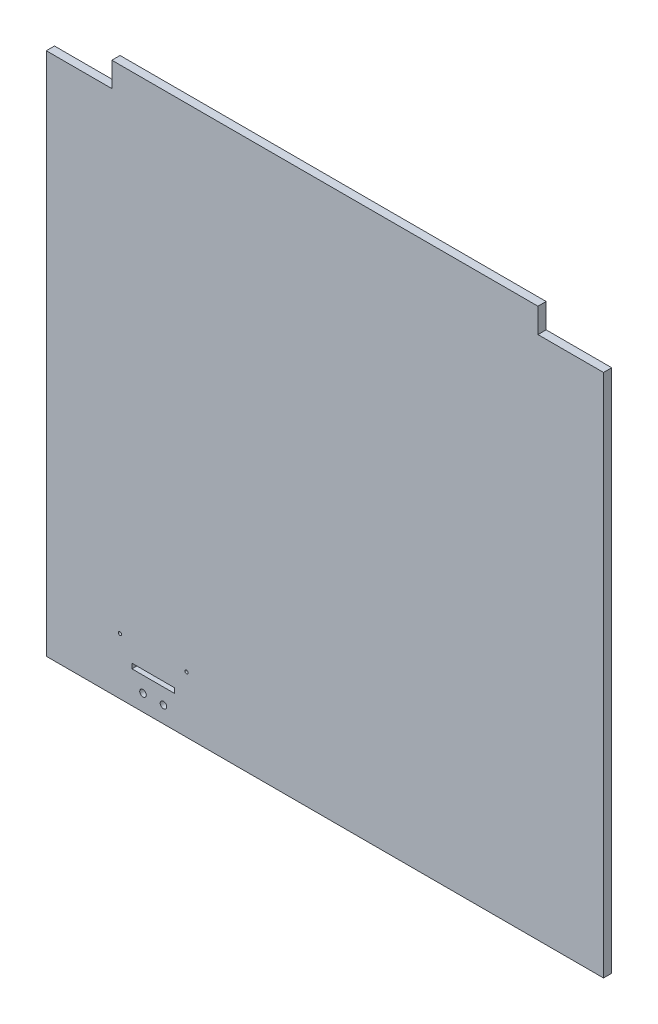
SolidWorks part; units mm, degrees
ref_plane "Plan de face" through (0, 0, 0) normal (0, 0, 1) x (1, 0, 0)
ref_plane "Plan de dessus" through (0, 0, 0) normal (0, 1, 0) x (1, 0, 0)
ref_plane "Plan de droite" through (0, 0, 0) normal (1, 0, 0) x (0, 0, -1)
sketch "Esquisse1" plane through (0, 0, 0) normal (0, 0, 1) x (1, 0, 0)
  line L1 (-340, 335) -> (340, 335)
  line L2 (-340, 335) -> (-340, -335)
  line L3 (-340, -335) -> (340, -335)
  line L4 (340, 335) -> (340, -335)
  dimension "D1" = 680
  dimension "D2" = 340
  dimension "D3" = 670
  dimension "D4" = 335
extrude "Boss.-Extru.1" add sketch "Esquisse1" along normal blind 10
sketch "Esquisse2" plane through (0, 0, 10) normal (0, 0, 1) x (1, 0, 0)
  line L0 (340, 335) -> (-340, 335) construction
  line L1 (-340, 335) -> (-260, 335)
  line L2 (-340, 335) -> (-340, 305)
  line L3 (-340, 305) -> (-260, 305)
  line L4 (-260, 335) -> (-260, 305)
  line L5 (340, 335) -> (260, 335)
  line L6 (340, 335) -> (340, 305)
  line L7 (340, 305) -> (260, 305)
  line L8 (260, 335) -> (260, 305)
  dimension "D1" = 30
  dimension "D2" = 30
  dimension "D3" = 80
  dimension "D4" = 80
extrude "Enlèv. mat.-Extru.1" cut sketch "Esquisse2" against normal through all
sketch "Esquisse3" plane through (0, 0, 10) normal (0, 0, 1) x (1, 0, 0)
  line L1 (-235.5, -290) -> (-183.5, -290)
  line L2 (-235.5, -290) -> (-235.5, -296)
  line L3 (-235.5, -296) -> (-183.5, -296)
  line L4 (-183.5, -290) -> (-183.5, -296)
  line L6 (-340, -335) -> (340, -335) construction
  line L7 (-340, 305) -> (-340, -335) construction
  dimension "D1" = 6
  dimension "D2" = 104.5
  dimension "D3" = 52
  dimension "D5" = 39
extrude "Enlèv. mat.-Extru.2" cut sketch "Esquisse3" against normal through all
sketch "Esquisse4" plane through (0, 0, 10) normal (0, 0, 1) x (1, 0, 0)
  line L0 (-340, -335) -> (340, -335) construction
  line L1 (-340, 305) -> (-340, -335) construction
  line L2 (340, -335) -> (340, 305) construction
  circle A0 centre (-222, -315) radius 4
  circle A1 centre (-197, -315) radius 4
  dimension "D1" = 8
  dimension "D2" = 8
  dimension "D3" = 25
  dimension "D4" = 20
  dimension "D5" = 20
  dimension "D6" = 118
  dimension "D7" = 537
extrude "Enlèv. mat.-Extru.3" cut sketch "Esquisse4" against normal through all
sketch "Esquisse5" plane through (0, 0, 10) normal (0, 0, 1) x (1, 0, 0)
  line L0 (-340, -335) -> (340, -335) construction
  line L1 (-340, 305) -> (-340, -335) construction
  line L3 (340, -335) -> (340, 305) construction
  circle A0 centre (-250, -266) radius 2
  circle A1 centre (-169, -266) radius 2
  dimension "D1" = 4
  dimension "D2" = 4
  dimension "D3" = 81
  dimension "D4" = 69
  dimension "D5" = 90
  dimension "D6" = 509
  dimension "D7" = 69
extrude "Enlèv. mat.-Extru.4" cut sketch "Esquisse5" against normal through all
